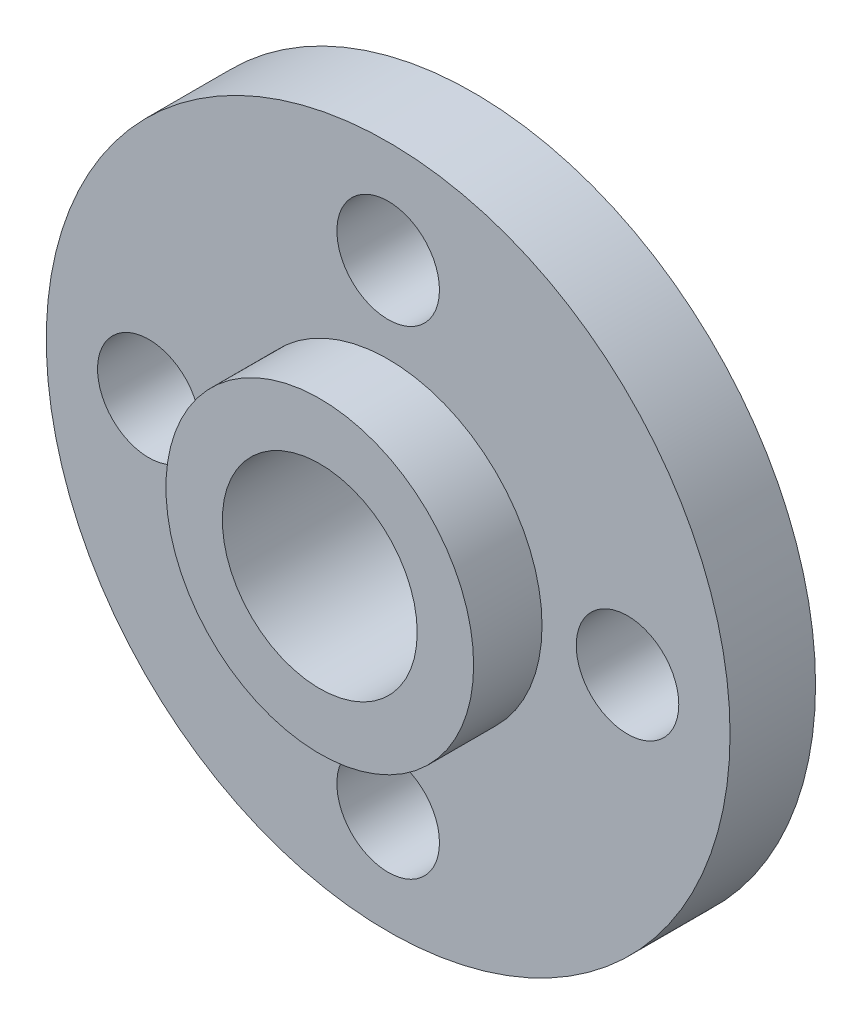
SolidWorks part; units mm, degrees
ref_plane "Plan de face" through (0, 0, 0) normal (0, 0, 1) x (1, 0, 0)
ref_plane "Plan de dessus" through (0, 0, 0) normal (0, 1, 0) x (1, 0, 0)
ref_plane "Plan de droite" through (0, 0, 0) normal (1, 0, 0) x (0, 0, -1)
sketch "Esquisse1" plane through (0, 0, 0) normal (0, 0, 1) x (1, 0, 0)
  circle A0 centre (0, 0) radius 10
  circle A1 centre (0, 0) radius 2.85
  dimension "D1" = 20
  dimension "D2" = 5.7
extrude "Boss.-Extru.1" add sketch "Esquisse1" along normal blind 2.5
sketch "Esquisse2" plane through (0, 0, 2.5) normal (0, 0, 1) x (1, 0, 0)
  circle A0 centre (0, 0) radius 4.5
  circle A1 centre (0, 0) radius 2.85 construction
  circle A2 centre (0, 0) radius 2.85
  dimension "D1" = 9
extrude "Boss.-Extru.2" add sketch "Esquisse2" along normal blind 2
sketch "Esquisse3" plane through (0, 0, 2.5) normal (0, 0, 1) x (1, 0, 0)
  circle A0 centre (0, 7) radius 1.5
  circle A1 centre (0, -7) radius 1.5
  circle A2 centre (7, 0) radius 1.5
  circle A3 centre (-7, 0) radius 1.5
  circle A4 centre (0, 0) radius 7 construction
  dimension "D1" = 3
  dimension "D2" = 14
extrude "Enlèv. mat.-Extru.1" cut sketch "Esquisse3" against normal through all
